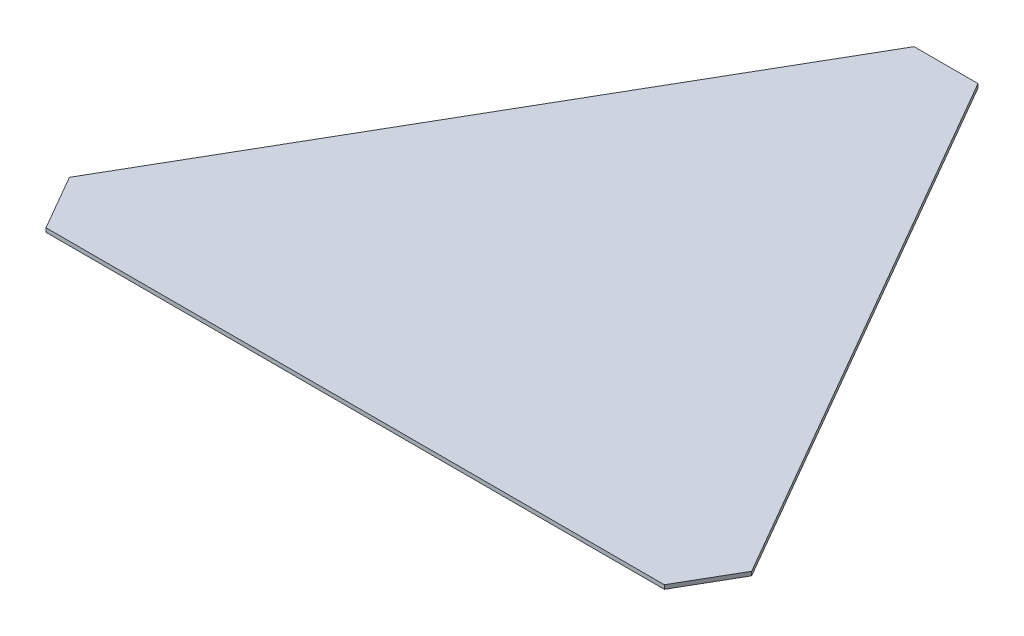
SolidWorks part; units mm, degrees
ref_plane "Alzado" through (0, 0, 0) normal (0, 0, 1) x (1, 0, 0)
ref_plane "Planta" through (0, 0, 0) normal (0, 1, 0) x (1, 0, 0)
ref_plane "Vista lateral" through (0, 0, 0) normal (1, 0, 0) x (0, 0, -1)
sketch "Croquis1" plane through (0, 0, 0) normal (0, 1, 0) x (1, 0, 0)
  line L0 (0, 0) -> (0, 470) construction
  line L1 (-40, 470) -> (40, 470)
  line L2 (0, 0) -> (407.0319, -235) construction
  line L3 (427.0319, -200.359) -> (387.0319, -269.641)
  line L4 (0, 0) -> (-407.0319, -235) construction
  line L5 (-387.0319, -269.641) -> (-427.0319, -200.359)
  line L6 (-40, 470) -> (-427.0319, -200.359)
  line L7 (-387.0319, -269.641) -> (387.0319, -269.641)
  line L8 (427.0319, -200.359) -> (40, 470)
  circle A0 centre (0, 0) radius 470 construction
  point P7 (0, 470)
  point P16 (0, 0)
  dimension "D1" = 470
  dimension "D2" = 80
  dimension "D3" = 3
extrude "Saliente-Extruir1" add sketch "Croquis1" along normal blind 5
